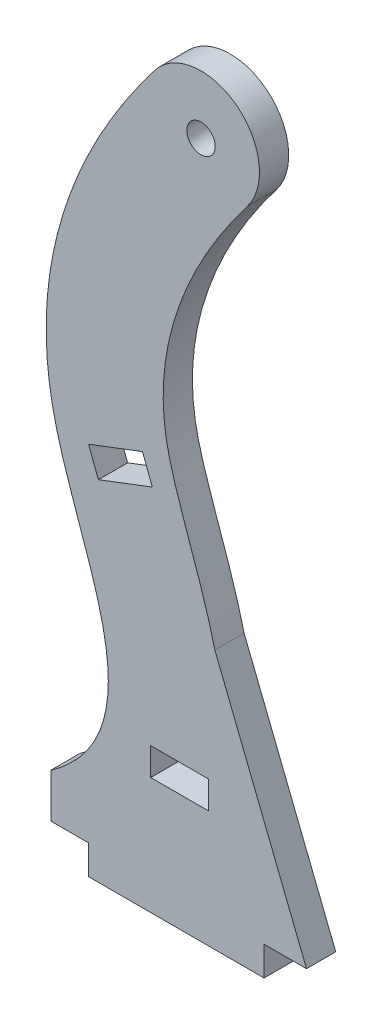
SolidWorks part; units mm, degrees
ref_plane "Front Plane" through (0, 0, 0) normal (0, 0, 1) x (1, 0, 0)
ref_plane "Top Plane" through (0, 0, 0) normal (0, 1, 0) x (1, 0, 0)
ref_plane "Right Plane" through (0, 0, 0) normal (1, 0, 0) x (0, 0, -1)
sketch "Sketch1" plane through (0, 0, 0) normal (0, 0, 1) x (1, 0, 0)
  line L0 (0, 0) -> (8.1706, 0)
  line L1 (0, 0) -> (0, 152.4) construction
  line L2 (8.1706, 74.9559) -> (10.3104, 69.3564)
  line L3 (42.6515, 136.9269) -> (22.5084, 152.4) construction
  line L4 (10.3104, 69.3564) -> (22.0076, 73.8263)
  line L5 (8.1706, 74.9559) -> (19.8678, 79.4258)
  line L6 (19.8678, 79.4258) -> (22.0076, 73.8263)
  line L7 (8.1706, 0) -> (8.1706, -6.35)
  line L8 (8.1706, -6.35) -> (46.2706, -6.35)
  line L9 (46.2706, -6.35) -> (46.2706, 0)
  line L10 (0, 9.5897) -> (0, 0)
  line L15 (46.2706, 0) -> (55.4886, 0)
  line L16 (21.6637, 25.0331) -> (34.1859, 25.0331)
  line L17 (21.6637, 25.0331) -> (21.6637, 19.0387)
  line L18 (21.6637, 19.0387) -> (34.1859, 19.0387)
  line L19 (34.1859, 25.0331) -> (34.1859, 19.0387)
  arc A0 (42.6515, 136.9269) -> (22.5084, 152.4) centre (32.58, 144.6635) ccw
  circle A1 centre (32.58, 144.6635) radius 3.0861
  spline S0 degree 3 poles (0, 9.5897) (16.9507, 21.5437) (11.3621, 46.5973) (-7.6363, 94.064) (3.9414, 128.2292) (22.5084, 152.4) knots 0 0 0 0 0.312819 0.48028 1 1 1 1
  spline S1 degree 1 poles (14.6386, -11.1677) (42.6515, 136.9269) knots 0 0 1 1 construction
  spline S2 degree 3 poles (14.6386, -11.1677) (15.9937, -10.2121) (18.6403, -8.1941) (23.5424, -3.7869) (28.8938, 2.4655) (33.6864, 10.9104) (36.6379, 19.7198) (37.9073, 28.2753) (37.8946, 37.5742) (36.6429, 45.8141) (34.5823, 54.1219) (31.9574, 62.3483) (29.4491, 69.3392) (27.5788, 74.8013) (26.4239, 78.4799) (25.5549, 81.7287) (24.7882, 85.4837) (24.2844, 90.3086) (24.4282, 96.2034) (25.3276, 102.3545) (27.0297, 108.788) (29.5776, 115.5054) (32.4312, 121.3091) (35.1581, 126.0488) (37.4241, 129.6434) (39.4976, 132.6682) (41.2617, 135.0957) (42.1865, 136.3215) (42.6515, 136.9269) knots 0 0 0 0 0.015625 0.03125 0.0625 0.09375 0.125 0.15625 0.1875 0.234812 0.266062 0.3125 0.375 0.40625 0.4375 0.46875 0.5 0.5625 0.625 0.6875 0.75 0.8125 0.875 0.90625 0.9375 0.96875 0.984375 1 1 1 1 only from (35.5939, 49.9715) to (42.6515, 136.9269)
  spline S3 degree 1 poles (35.5939, 49.9715) (55.4886, 0) knots 0 0 1 1
  point P3 (0, 80.1188)
  point P5 (0, 9.5897)
  point P7 (12.4584, 32.321)
  point P8 (8.1706, 53.2226)
  point P10 (22.5084, 152.4)
  point P12 (55.4886, 0)
  point P15 (35.5939, 49.9715)
  dimension "D1" = 6.1722
  dimension "D2" = 152.4
  dimension "D4" = 5.9944
  dimension "D5" = 12.5222
  dimension "D6" = 38.1
  dimension "D7" = 6.35
  dimension "D10" = 12.5222
  dimension "D11" = 5.9944
  dimension "D3" = 25.4
extrude "Boss-Extrude1" add sketch "Sketch1" along normal blind 6.35
